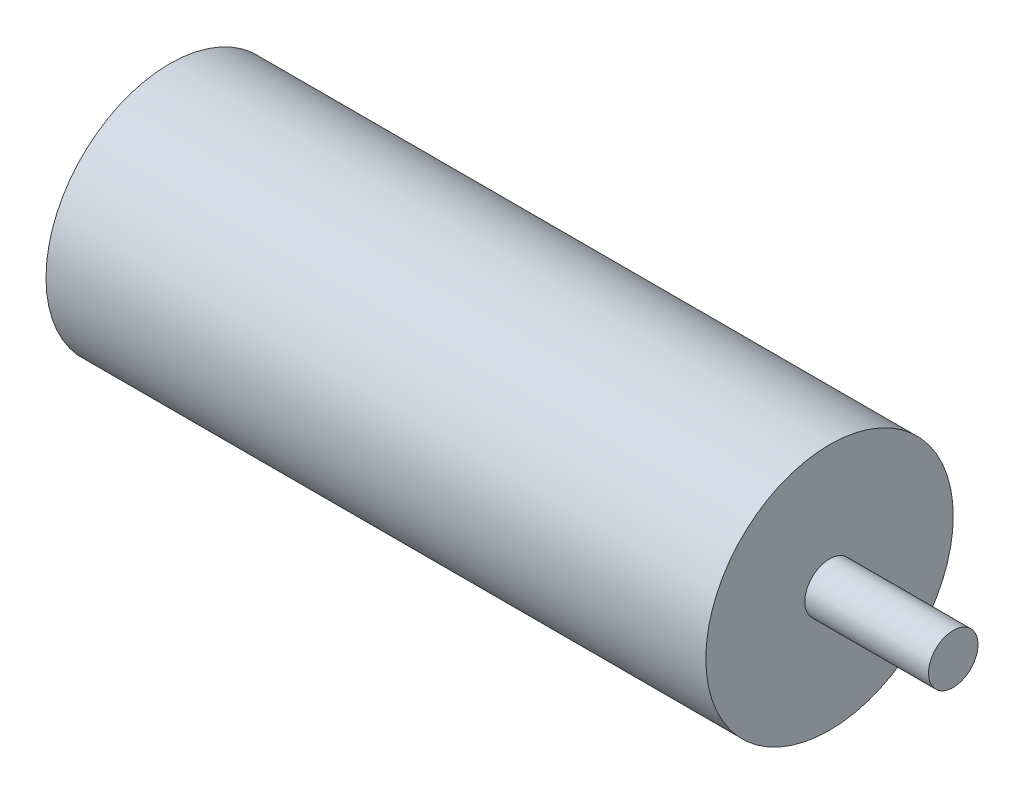
SolidWorks part; units mm, degrees
ref_plane "Front Plane" through (0, 0, 0) normal (0, 0, 1) x (1, 0, 0)
ref_plane "Top Plane" through (0, 0, 0) normal (0, 1, 0) x (1, 0, 0)
ref_plane "Right Plane" through (0, 0, 0) normal (1, 0, 0) x (0, 0, -1)
sketch "Sketch1" plane through (0, 0, 0) normal (1, 0, 0) x (0, 0, -1)
  circle A0 centre (-35.8177, 20.0994) radius 7.5
  dimension "D1" = 15
extrude "Boss-Extrude1" add sketch "Sketch1" along normal blind 45
sketch "Sketch2" plane through (45, 0, 0) normal (1, 0, 0) x (0, 0, -1)
  circle A0 centre (-35.8177, 20.0994) radius 1.5
extrude "Boss-Extrude2" add sketch "Sketch2" along normal blind 15
sketch "Sketch3" plane through (0, 0, 0) normal (-1, 0, 0) x (0, 0, 1)
  circle A0 centre (35.9464, 19.4738) radius 19.3102
extrude "Cut-Extrude1" cut sketch "Sketch3" against normal blind 5
sketch "Sketch4" plane through (60, 0, 0) normal (1, 0, 0) x (0, 0, -1)
  circle A0 centre (-35.8446, 20.1075) radius 8.7411
extrude "Cut-Extrude2" cut sketch "Sketch4" against normal blind 7.5
